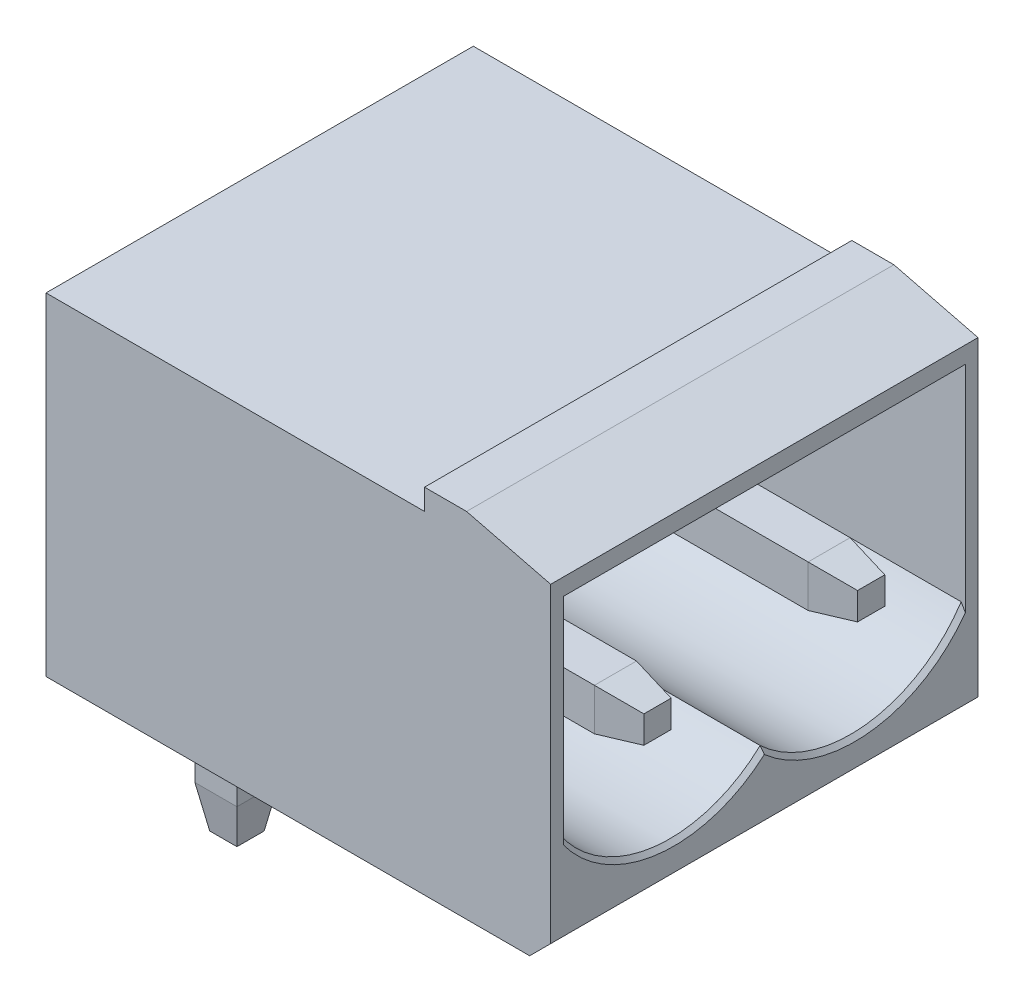
SolidWorks part; units mm, degrees
ref_plane "Ebene vorne" through (0, 0, 0) normal (0, 0, 1) x (1, 0, 0)
ref_plane "Ebene oben" through (0, 0, 0) normal (0, 1, 0) x (1, 0, 0)
ref_plane "Ebene rechts" through (0, 0, 0) normal (1, 0, 0) x (0, 0, -1)
sketch "Skizze3" plane through (0, 0, 0) normal (0, 0, 1) x (1, 0, 0)
  line L1 (6, -3.95) -> (-6, -3.95)
  line L2 (6, -3.95) -> (6, 3.95)
  line L3 (6, 3.95) -> (-6, 3.95)
  line L4 (-6, -3.95) -> (-6, 3.95)
  line L5 (6, -3.95) -> (-6, 3.95) construction
  line L6 (6, 3.95) -> (-6, -3.95) construction
  point P0 (0, 0)
  dimension "D1" = 12
  dimension "D2" = 7.9
extrude "Aufsatz-Linear austragen2" add sketch "Skizze3" along normal blind 10.16
sketch "Skizze4" plane through (0, 0, 10.16) normal (0, 0, 1) x (1, 0, 0)
  line L0 (3, 3.95) -> (3, 4.45)
  line L1 (6, 3.95) -> (-6, 3.95) construction
  line L2 (3, 4.45) -> (4, 4.45)
  line L3 (4, 4.45) -> (6, 3.95)
  line L4 (6, 3.95) -> (3, 3.95)
  line L5 (-6, -3.95) -> (6, -3.95) construction
  dimension "D1" = 8.4
  dimension "D2" = 3
  dimension "D3" = 1
extrude "Aufsatz-Linear austragen3" add sketch "Skizze4" against normal through all
sketch "Skizze5" plane through (6, 0, 0) normal (1, 0, 0) x (0, 0, -1)
  line L0 (-9.86, 3.45) -> (-9.86, -1.39)
  line L1 (-9.86, 3.45) -> (-0.3, 3.45)
  line L2 (-5.08, 3.45) -> (-5.08, 3.95) construction
  line L3 (-9.86, -1.39) -> (-0.3, -1.39) construction
  line L4 (-10.16, 3.95) -> (0, 3.95) construction
  line L5 (-5.08, 3.45) -> (-5.08, -1.96) construction
  line L6 (-0.3, 3.45) -> (-0.3, -1.39)
  line L7 (-10.16, -3.95) -> (-10.16, 3.95) construction
  arc A0 (-9.86, -1.39) -> (-5.08, -1.96) centre (-7.2294, 0.3427) ccw
  arc A2 (-0.3, -1.39) -> (-5.08, -1.96) centre (-2.9306, 0.3427) cw
  dimension "D3" = 3.15
  dimension "D1" = 0.3
  dimension "D2" = 0.5
  dimension "D4" = 4.84
  dimension "D5" = 0.57
extrude "Schnitt-Linear austragen1" cut sketch "Skizze5" against normal offset from surface (9 mm away) 3 up to face at (-6, 0, 5.08)
sketch "Skizze6" plane through (0, -3.95, 0) normal (0, -1, 0) x (-1, 0, 0)
  line L10 (4, -7.62) -> (4, -8.12) construction
  line L11 (4.5, -7.12) -> (3.5, -7.12)
  line L12 (4.5, -7.12) -> (4.5, -8.12)
  line L13 (4.5, -8.12) -> (3.5, -8.12)
  line L14 (3.5, -7.12) -> (3.5, -8.12)
  line L15 (3.5, -8.12) -> (4.5, -7.12) construction
  line L16 (4.5, -8.12) -> (3.5, -7.12) construction
  line L17 (6, -5.08) -> (-6, -5.08) construction
  line L18 (6, -10.16) -> (6, 0) construction
  line L19 (-6, -10.16) -> (-6, 0) construction
  line L20 (4.5, -2.04) -> (3.5, -3.04) construction
  line L21 (3.5, -2.04) -> (4.5, -3.04) construction
  line L22 (4, -2.54) -> (4, -2.04) construction
  line L23 (3.5, -3.04) -> (3.5, -2.04)
  line L24 (4.5, -2.04) -> (3.5, -2.04)
  line L25 (4.5, -3.04) -> (4.5, -2.04)
  line L26 (4.5, -3.04) -> (3.5, -3.04)
  dimension "D1" = 1
  dimension "D2" = 10
  dimension "D3" = 5.08
extrude "Aufsatz-Linear austragen4" add sketch "Skizze6" along normal blind 3.45
sketch "Skizze7" plane through (-3, 0, 0) normal (1, 0, 0) x (0, 0, -1)
  line L0 (-7.62, -0.15) -> (-8.12, -0.15) construction
  line L1 (-8.12, -0.65) -> (-7.12, -0.65)
  line L2 (-8.12, -0.65) -> (-8.12, 0.35)
  line L3 (-8.12, 0.35) -> (-7.12, 0.35)
  line L4 (-7.12, -0.65) -> (-7.12, 0.35)
  line L5 (-8.12, -0.65) -> (-7.12, 0.35) construction
  line L6 (-7.62, -0.15) -> (-7.62, -0.65) construction
  line L7 (-7.62, -0.65) -> (-7.62, -7.4) construction
  line L8 (-7.12, -7.4) -> (-8.12, -7.4) construction
  line L9 (-10.16, -3.95) -> (0, -3.95) construction
  line L10 (-5.08, -1.96) -> (-5.08, 3.45) construction
  line L11 (-0.3, 3.45) -> (-9.86, 3.45) construction
  line L12 (-3.04, -0.65) -> (-3.04, 0.35)
  line L13 (-2.04, 0.35) -> (-3.04, 0.35)
  line L14 (-2.04, -0.65) -> (-2.04, 0.35)
  line L15 (-2.04, -0.65) -> (-3.04, -0.65)
  point P0 (-7.1161, 0.3539)
  dimension "D1" = 1
  dimension "D2" = 3.8
extrude "Aufsatz-Linear austragen5" add sketch "Skizze7" along normal up to surface (9 mm away) up to face at (6, -0.012, 5.08)
chamfer "Fase1" distance 1 angle 10 8 edges at (-4, -7.4, 7.12) (-4.5, -7.4, 7.62) (-4, -7.4, 8.12) (-3.5, -7.4, 7.62) (-4, -7.4, 3.04) (-3.5, -7.4, 2.54) (-4, -7.4, 2.04) (-4.5, -7.4, 2.54)
chamfer "Fase14" distance 1 angle 10 8 edges at (6, -0.15, 7.12) (6, -0.65, 7.62) (6, -0.15, 8.12) (6, 0.35, 7.62) (6, -0.65, 2.54) (6, -0.15, 3.04) (6, 0.35, 2.54) (6, -0.15, 2.04)
chamfer "Fase15" distance 0.1 angle 45 3 edges at (6, -2.7851, 7.6024) (6, -2.7851, 2.5576) (6, 3.45, 5.08)
chamfer "Fase16" distance 0.5 angle 45 1 edges at (6, -3.95, 5.08)
